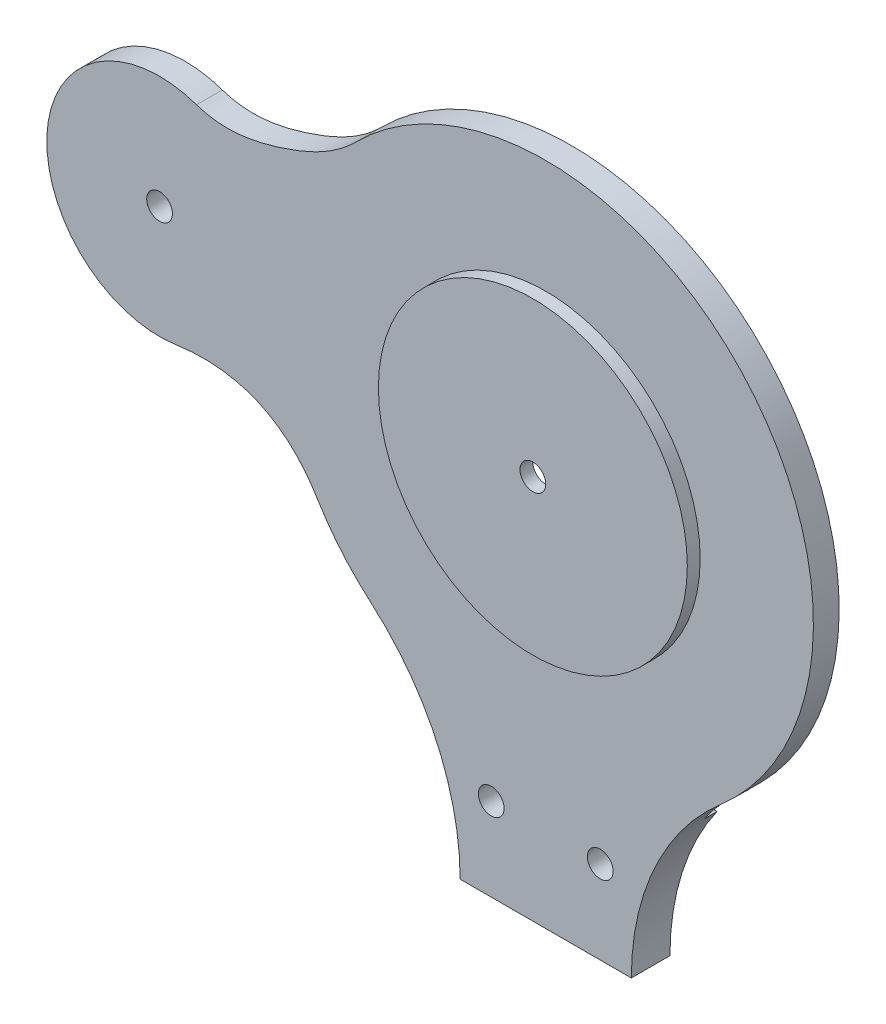
SolidWorks part; units mm, degrees
ref_plane "Front Plane" through (0, 0, 0) normal (0, 0, 1) x (1, 0, 0)
ref_plane "Top Plane" through (0, 0, 0) normal (0, 1, 0) x (1, 0, 0)
ref_plane "Right Plane" through (0, 0, 0) normal (1, 0, 0) x (0, 0, -1)
sketch "Sketch1" plane through (0, 0, 0) normal (0, 0, 1) x (1, 0, 0)
  line L0 (-16.891, -131.2827) -> (16.891, -131.2827)
  circle A0 centre (0, -52.8237) radius 24.4551
  arc A1 (34.5065, -92.8193) -> (-34.5065, -92.8193) centre (0, -52.8237) ccw
  arc A4 (34.5065, -92.8193) -> (16.891, -131.2827) centre (67.691, -131.2827) ccw
  arc A5 (-16.891, -131.2827) -> (-34.5065, -92.8193) centre (-67.691, -131.2827) ccw
  circle A6 centre (-10.7564, -114.872) radius 2.54
  circle A7 centre (10.7564, -114.872) radius 2.54
extrude "Boss-Extrude1" add sketch "Sketch1" along normal blind 5.08
sketch "Sketch4" plane through (0, 0, 5.08) normal (0, 0, 1) x (1, 0, 0)
  circle A0 centre (0, -52.8237) radius 30.48
extrude "Boss-Extrude3" add sketch "Sketch4" along normal blind 2.54
sketch "Sketch5" plane through (0, 0, 7.62) normal (0, 0, 1) x (1, 0, 0)
  circle A0 centre (0, -52.8237) radius 2.54
extrude "Cut-Extrude2" cut sketch "Sketch5" against normal through all
sketch "Sketch6" plane through (0, 0, 0) normal (0, 0, -1) x (-1, 0, 0)
  line L0 (16.891, -131.2827) -> (-16.891, -131.2827) construction
  line L1 (16.891, -131.2827) -> (-16.891, -131.2827)
  line L2 (-26.1953, -101.9783) -> (26.1953, -101.9783)
  circle A0 centre (0, -52.8237) radius 45.336
  circle A1 centre (0, -52.8237) radius 37.9584
  arc A2 (-16.891, -131.2827) -> (-34.5065, -92.8193) centre (-67.691, -131.2827) ccw construction
  arc A3 (34.5065, -92.8193) -> (16.891, -131.2827) centre (67.691, -131.2827) ccw construction
  arc A4 (-16.891, -131.2827) -> (-26.1953, -101.9783) centre (-67.691, -131.2827) ccw
  arc A5 (26.1953, -101.9783) -> (16.891, -131.2827) centre (67.691, -131.2827) ccw
extrude "Boss-Extrude4" add sketch "Sketch6" along normal blind 2.54
sketch "Sketch7" plane through (0, 0, 0) normal (0, 0, 1) x (1, 0, 0)
  circle A0 centre (-10.7564, -114.872) radius 2.54
  circle A1 centre (10.7564, -114.872) radius 2.54
extrude "Cut-Extrude3" cut sketch "Sketch7" against normal through all
sketch "Sketch10" plane through (0, 0, 5.08) normal (0, 0, 1) x (1, 0, 0)
  line L0 (0, 0) -> (0, -131.2827) construction
  line L1 (-16.891, -131.2827) -> (16.891, -131.2827) construction
  arc A0 (-68.9002, -24.9499) -> (-72.9914, -67.9939) centre (-76.2, -45.9725) ccw
  arc A2 (34.5065, -92.8193) -> (-34.5065, -92.8193) centre (0, -52.8237) ccw construction
  arc A4 (34.5065, -92.8193) -> (0, 0) centre (0, -52.8237) ccw
  arc A5 (-37.5246, -15.6451) -> (-45.1618, -80.2237) centre (0, -52.8237) ccw
  spline S0 degree 3 poles (-72.9914, -67.9939) (-65.5082, -66.9035) (-55.0334, -68.6407) (-47.5743, -76.2473) (-45.1618, -80.2237) knots 0 0 0 0 0.604505 1 1 1 1
  spline S1 degree 3 poles (-68.9002, -24.9499) (-63.2972, -26.8954) (-51.3897, -24.4152) (-41.5693, -19.7274) (-37.5246, -15.6451) knots 0 0 0 0 0.52007 1 1 1 1
  arc M7 (34.5065, -92.8193) -> (-34.5065, -92.8193) centre (0, -52.8237) ccw
  dimension "D1" = 76.2
extrude "Boss-Extrude6" add sketch "Sketch10" against normal up to surface (5.08 mm away) contours S1 A0 S0 M7 up to face at (45.336, -52.8237, 0)
sketch "Sketch11" plane through (0, 0, 5.08) normal (0, 0, 1) x (1, 0, 0)
  circle A0 centre (-76.2, -45.9725) radius 2.54
extrude "Cut-Extrude4" cut sketch "Sketch11" against normal through all
